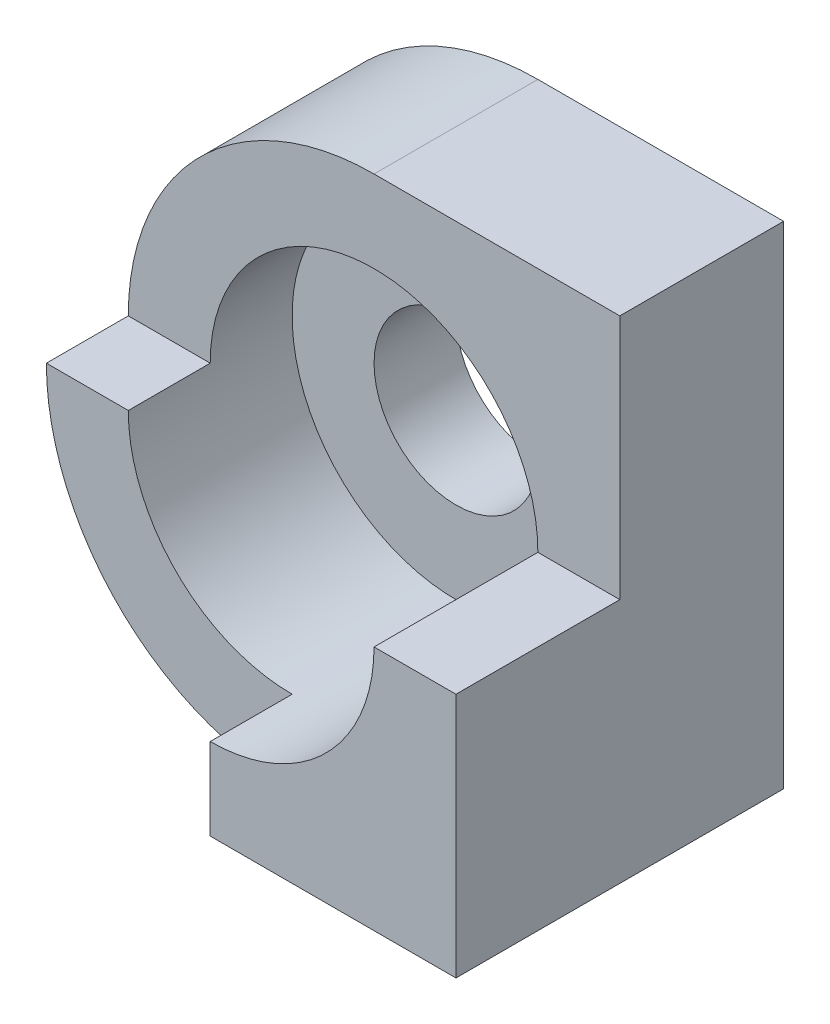
SolidWorks part; units mm, degrees
ref_plane "Front" through (0, 0, 0) normal (0, 0, 1) x (1, 0, 0)
ref_plane "Top" through (0, 0, 0) normal (0, 1, 0) x (1, 0, 0)
ref_plane "Right" through (0, 0, 0) normal (1, 0, 0) x (0, 0, -1)
sketch "Sketch1" plane through (0, 0, 0) normal (0, 0, 1) x (1, 0, 0)
  line L0 (3, 0) -> (3, 3)
  line L1 (3, 3) -> (0, 3)
  line L2 (3, 0) -> (3, -3)
  line L3 (3, -3) -> (0, -3)
  arc A0 (0, 3) -> (0, -3) centre (0, 0) ccw
  circle A1 centre (0, 0) radius 1
  dimension "D1" = 3
  dimension "D2" = 2
extrude "Boss-Extrude1" add sketch "Sketch1" along normal blind 2
sketch "Sketch2" plane through (0, 0, 2) normal (0, 0, 1) x (1, 0, 0)
  circle A0 centre (0, 0) radius 2
  dimension "D1" = 4
extrude "Cut-Extrude1" cut sketch "Sketch2" against normal blind 1 contours A0
sketch "Sketch3" plane through (0, 0, 2) normal (0, 0, 1) x (1, 0, 0)
  line L0 (0, -2) -> (0, -3)
  line L1 (0, -3) -> (3, -3)
  line L2 (3, -3) -> (3, 0)
  line L3 (3, -3) -> (3, 3) construction
  line L4 (3, 0) -> (2, 0)
  arc A0 (2, 0) -> (0, -2) centre (0, 0) cw
  circle A1 centre (0, 0) radius 2 construction
  circle A2 centre (0, 0) radius 2 construction
extrude "Boss-Extrude2" add sketch "Sketch3" along normal blind 2
sketch "Sketch4" plane through (0, 0, 2) normal (0, 0, 1) x (1, 0, 0)
  line L0 (-3, 0) -> (-2, 0)
  line L1 (0, -2) -> (0, -3)
  arc A0 (0, -2) -> (-2, 0) centre (0, 0) cw
  arc A1 (2, 0) -> (0, -2) centre (0, 0) ccw construction
  circle A2 centre (0, 0) radius 2 construction
  arc A3 (0, -3) -> (-3, 0) centre (0, 0) cw
  arc A4 (0, 3) -> (0, -3) centre (0, 0) ccw construction
extrude "Boss-Extrude3" add sketch "Sketch4" along normal blind 1
